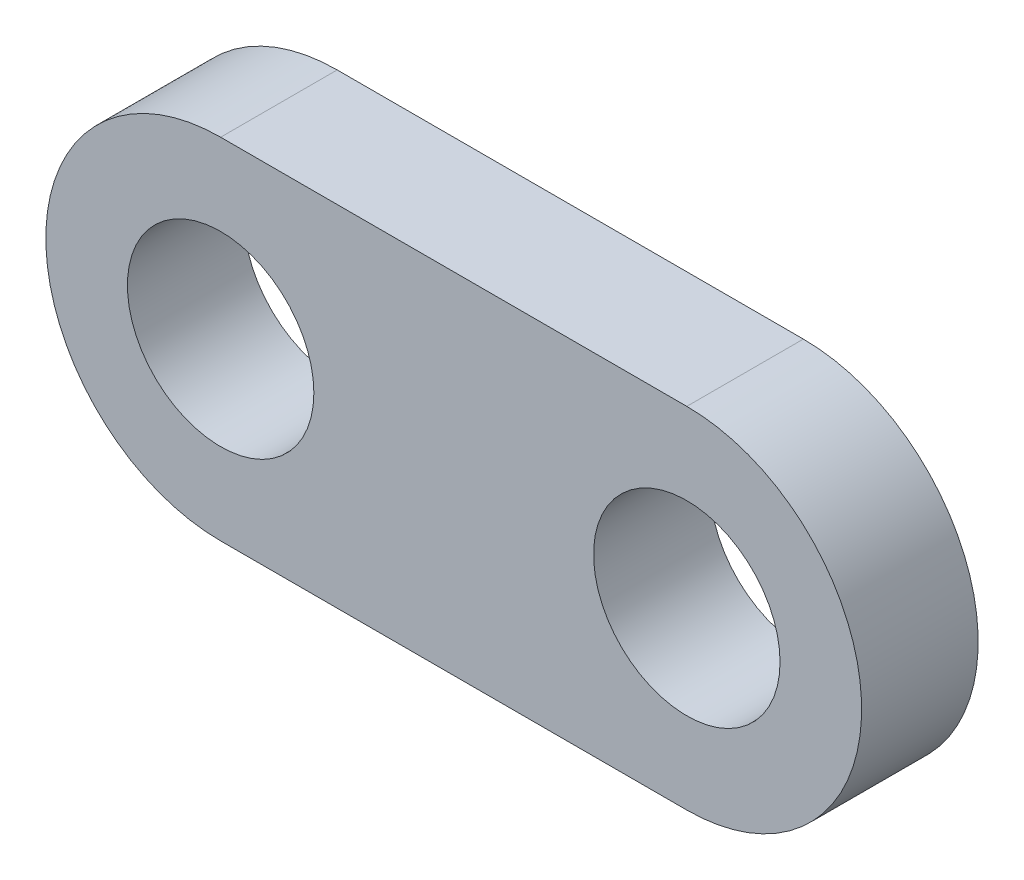
SolidWorks part; units mm, degrees
ref_plane "Front Plane" through (0, 0, 0) normal (0, 0, 1) x (1, 0, 0)
ref_plane "Top Plane" through (0, 0, 0) normal (0, 1, 0) x (1, 0, 0)
ref_plane "Right Plane" through (0, 0, 0) normal (1, 0, 0) x (0, 0, -1)
sketch "Sketch2" plane through (0, 0, 0) normal (0, 0, 1) x (1, 0, 0)
  line L0 (0, 7.5) -> (20, 7.5)
  line L1 (0, -7.5) -> (20, -7.5)
  circle A0 centre (0, 0) radius 4
  circle A1 centre (20, 0) radius 4
  arc A2 (0, 7.5) -> (0, -7.5) centre (0, 0) ccw
  arc A3 (20, -7.5) -> (20, 7.5) centre (20, 0) ccw
  dimension "D1" = 8
  dimension "D2" = 15
  dimension "D4" = 8
  dimension "D5" = 15
  dimension "D3" = 20
extrude "Boss-Extrude1" add sketch "Sketch2" against normal blind 5
